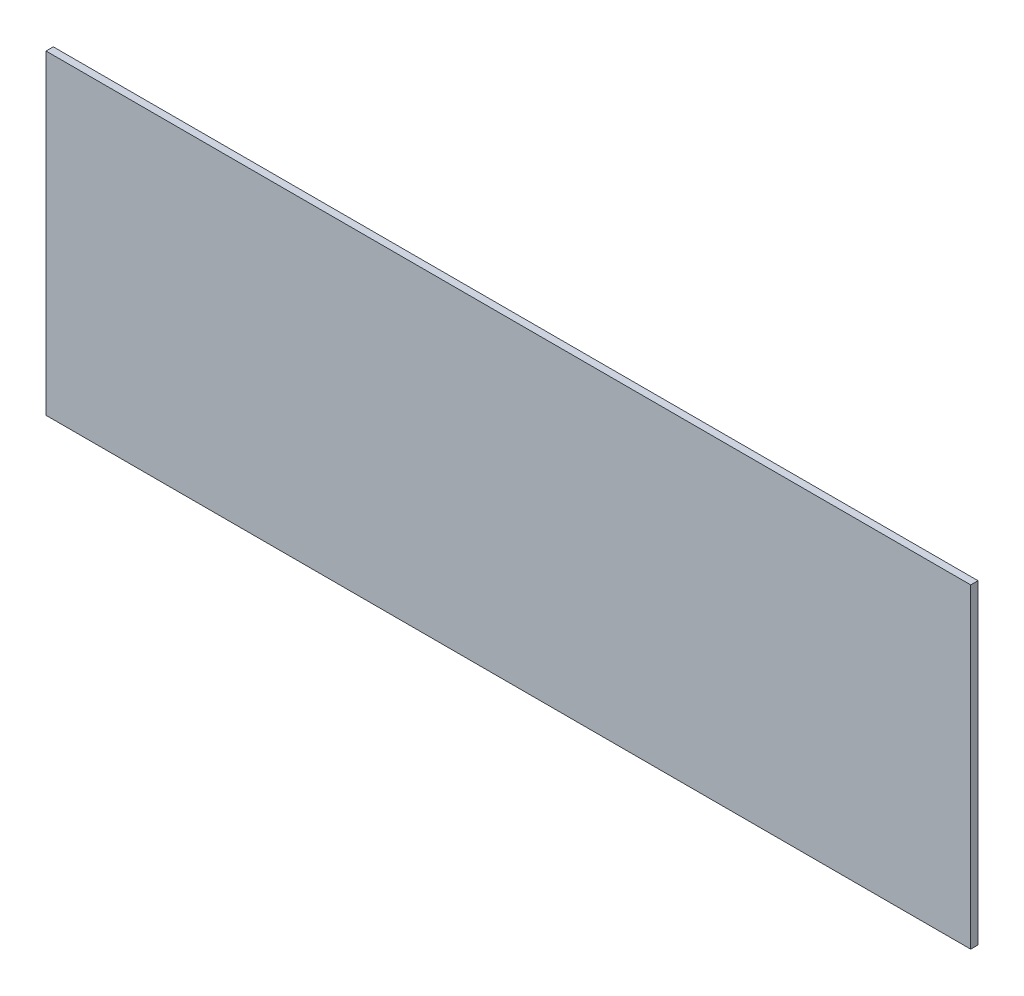
SolidWorks part; units mm, degrees
ref_plane "Front Plane" through (0, 0, 0) normal (0, 0, 1) x (1, 0, 0)
ref_plane "Top Plane" through (0, 0, 0) normal (0, 1, 0) x (1, 0, 0)
ref_plane "Right Plane" through (0, 0, 0) normal (1, 0, 0) x (0, 0, -1)
sketch "Sketch1" plane through (0, 0, 0) normal (0, 0, 1) x (1, 0, 0)
  line L1 (-95.25, 32.5) -> (95.25, 32.5)
  line L2 (-95.25, 32.5) -> (-95.25, -32.5)
  line L3 (-95.25, -32.5) -> (95.25, -32.5)
  line L4 (95.25, 32.5) -> (95.25, -32.5)
  line L5 (-95.25, 32.5) -> (95.25, -32.5) construction
  line L6 (-95.25, -32.5) -> (95.25, 32.5) construction
  point P0 (0, 0)
  dimension "D1" = 190.5
  dimension "D2" = 65
extrude "Boss-Extrude1" add sketch "Sketch1" along normal blind 1.5
